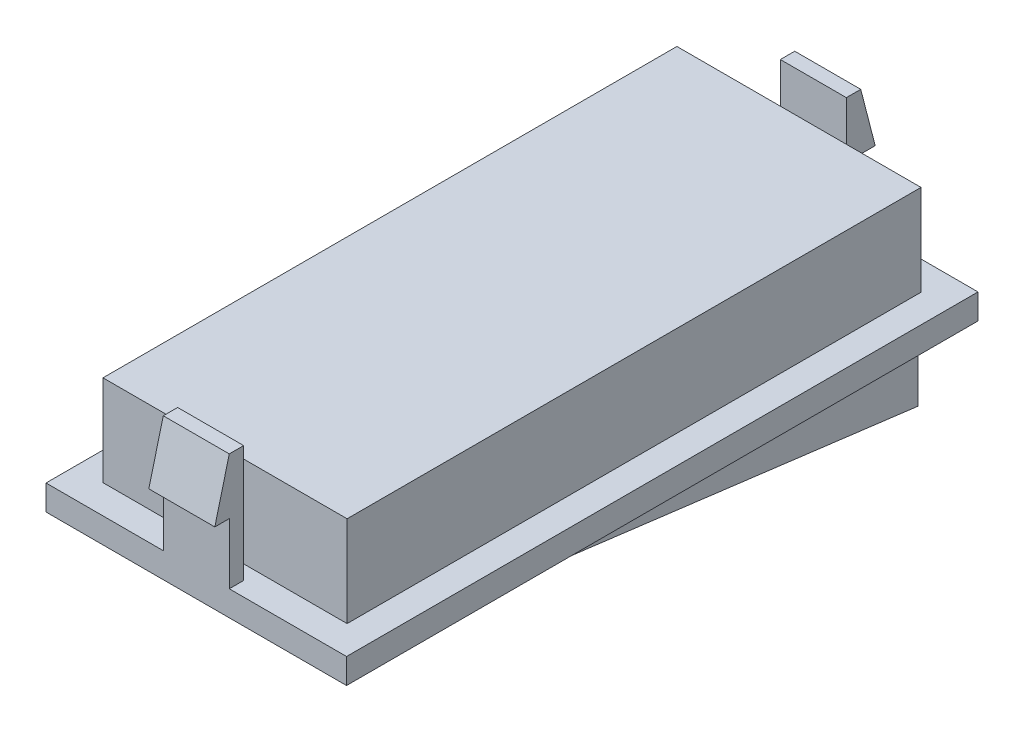
SolidWorks part; units mm, degrees
ref_plane "Front Plane" through (0, 0, 0) normal (0, 0, 1) x (1, 0, 0)
ref_plane "Top Plane" through (0, 0, 0) normal (0, 1, 0) x (1, 0, 0)
ref_plane "Right Plane" through (0, 0, 0) normal (1, 0, 0) x (0, 0, -1)
sketch "Sketch1" plane through (0, 0, 0) normal (0, 1, 0) x (1, 0, 0)
  line L1 (-12.065, -25.35) -> (12.065, -25.35)
  line L2 (-12.065, -25.35) -> (-12.065, 25.35)
  line L3 (-12.065, 25.35) -> (12.065, 25.35)
  line L4 (12.065, -25.35) -> (12.065, 25.35)
  line L5 (-12.065, -25.35) -> (12.065, 25.35) construction
  line L6 (-12.065, 25.35) -> (12.065, -25.35) construction
  point P0 (0, 0)
  dimension "D1" = 24.13
  dimension "D2" = 50.7
extrude "Boss-Extrude1" add sketch "Sketch1" along normal blind 2.02 contours L3 L4 L1 L2
sketch "Sketch2" plane through (0, 2.02, 0) normal (0, 1, 0) x (1, 0, 0)
  line L1 (-9.8, -23.04) -> (9.8, -23.04)
  line L2 (-9.8, -23.04) -> (-9.8, 23.04)
  line L3 (-9.8, 23.04) -> (9.8, 23.04)
  line L4 (9.8, -23.04) -> (9.8, 23.04)
  line L5 (-9.8, -23.04) -> (9.8, 23.04) construction
  line L6 (-9.8, 23.04) -> (9.8, -23.04) construction
  point P0 (0, 0)
  dimension "D1" = 46.08
  dimension "D2" = 19.6
extrude "Boss-Extrude2" add sketch "Sketch2" along normal blind 7.29
sketch "Sketch3" plane through (12.065, 0, 0) normal (1, 0, 0) x (0, 0, -1)
  line L0 (-22.8849, 0) -> (22.7813, -5.781)
  line L1 (-25.35, 0) -> (25.35, 0) construction
  line L2 (22.7813, -5.781) -> (22.7813, 0)
  line L3 (22.7813, 0) -> (-22.8849, 0)
extrude "Boss-Extrude3" add sketch "Sketch3" against normal up to surface (19.6 mm away) from surface at -2.265 up to face at (-9.8, 5.665, 0) starting at face at (9.8, 5.665, 0)
sketch "Sketch4" plane through (0, 0, -25.35) normal (0, 0, -1) x (-1, 0, 0)
  line L0 (12.065, 2.02) -> (-12.065, 2.02) construction
  line L2 (0, 0) -> (0, 18.5708) construction
  line L9 (-2.65, 11.4) -> (2.65, 11.4)
  line L10 (-2.65, 11.4) -> (-2.65, 2.02)
  line L11 (-2.65, 2.02) -> (2.65, 2.02)
  line L12 (2.65, 11.4) -> (2.65, 2.02)
  line L13 (-2.65, 11.4) -> (2.65, 2.02) construction
  line L14 (-2.65, 2.02) -> (2.65, 11.4) construction
  point P11 (0, 6.71)
  dimension "D1" = 5.3
  dimension "D2" = 9.38
extrude "Boss-Extrude4" add sketch "Sketch4" against normal blind 1.155
sketch "Sketch5" plane through (2.65, 0, 0) normal (1, 0, 0) x (0, 0, -1)
  line L0 (25.35, 11.4) -> (25.35, 6.9)
  line L1 (25.35, 11.4) -> (25.35, 2.02) construction
  line L2 (25.35, 6.9) -> (26.51, 6.9)
  line L3 (26.51, 6.9) -> (25.35, 11.4)
  dimension "D1" = 1.16
  dimension "D2" = 4.5
extrude "Boss-Extrude5" add sketch "Sketch5" against normal up to surface (5.3 mm away) up to face at (-2.65, 6.71, -24.7725)
mirror "Mirror1" about plane through (0, 0, 0) normal (0, 0, 1) of "Boss-Extrude4", "Boss-Extrude5"
